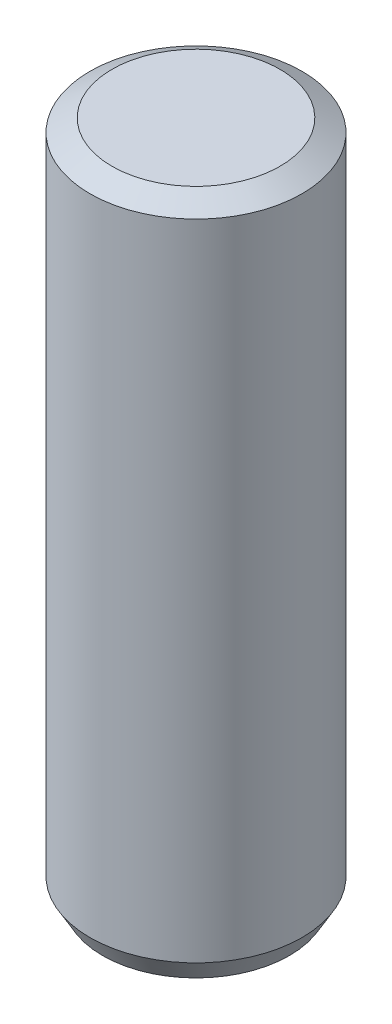
SolidWorks part; units mm, degrees
ref_plane "Front Plane" through (0, 0, 0) normal (0, 0, 1) x (1, 0, 0)
ref_plane "Top Plane" through (0, 0, 0) normal (0, 1, 0) x (1, 0, 0)
ref_plane "Right Plane" through (0, 0, 0) normal (1, 0, 0) x (0, 0, -1)
sketch "Sketch1" plane through (0, 0, 0) normal (0, 1, 0) x (1, 0, 0)
  circle A0 centre (0, 0) radius 2.5
  dimension "D1" = 5
extrude "Boss-Extrude1" add sketch "Sketch1" along normal blind 16
chamfer "Chamfer1" distance 0.3 angle 60 2 edges at (0, 0, 2.5) (0, 16, 2.5)
